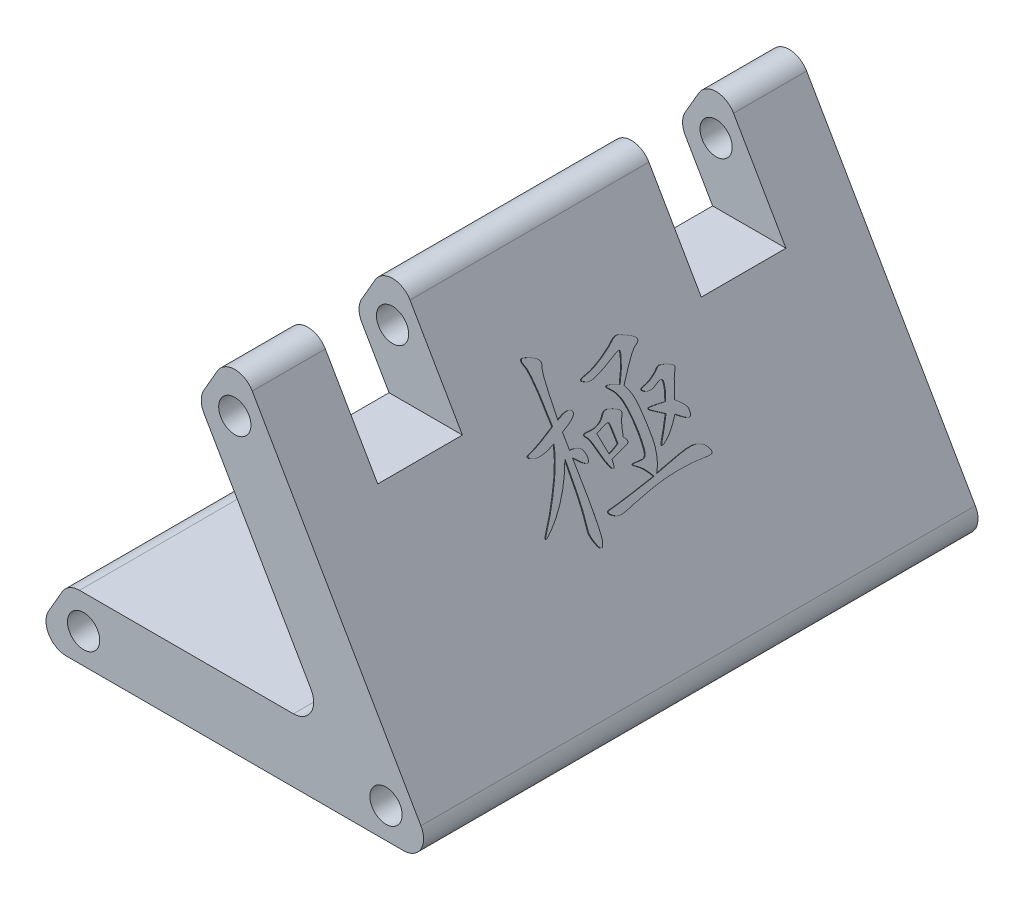
SolidWorks part; units mm, degrees
material "ABS"
ref_plane "前视基准面" through (0, 0, 0) normal (0, 0, 1) x (1, 0, 0)
ref_plane "上视基准面" through (0, 0, 0) normal (0, 1, 0) x (1, 0, 0)
ref_plane "右视基准面" through (0, 0, 0) normal (1, 0, 0) x (0, 0, -1)
sketch "草图1" plane through (0, 0, 0) normal (0, 0, 1) x (1, 0, 0)
  line L0 (0, 0) -> (-15, -25.9808) construction
  line L1 (-15, -25.9808) -> (15, -25.9808) construction
  line L2 (15, -25.9808) -> (0, 0) construction
  line L3 (20.1962, -28.9808) -> (0, 6)
  line L4 (0, 6) -> (-20.1962, -28.9808)
  line L5 (-20.1962, -28.9808) -> (20.1962, -28.9808)
  circle A0 centre (0, 0) radius 1.6
  circle A1 centre (-15, -25.9808) radius 1.6
  circle A2 centre (15, -25.9808) radius 1.6
  dimension "D3" = 3.2
  dimension "D1" = 30
  dimension "D2" = 3
extrude "凸台-拉伸1" add sketch "草图1" along normal mid plane 55
fillet "圆角1" radius 2 3 edges at (20.1962, -28.9808, 0) (-20.1962, -28.9808, 0) (0, 6, 0)
sketch "草图2" plane through (0, 0, -27.5) normal (0, 0, -1) x (-1, 0, 0)
  line L0 (3.6373, -0.3) -> (-9.2842, -22.6808)
  line L1 (1.7321, 3) -> (18.4641, -25.9808) construction
  line L2 (-9.2842, -22.6808) -> (16.5588, -22.6808)
  line L3 (16.5588, -22.6808) -> (3.6373, -0.3)
  line L4 (0, 0) -> (-15, -25.9808) construction
  circle A0 centre (15, -25.9808) radius 1.6 construction
  dimension "D1" = 3.3
  dimension "D2" = 3.3
extrude "切除-拉伸1" cut sketch "草图2" against normal mid plane 133
fillet "圆角2" radius 2 3 edges at (-16.5588, -22.6808, 0) (9.2842, -22.6808, 0) (-3.6373, -0.3, 0)
sketch "草图3" plane through (2.5981, 1.5, 0) normal (0.866, 0.5, 0) x (0, 0, -1)
  line L0 (-27.5, -19.7321) -> (27.5, -19.7321) construction
  line L1 (-27.5, -31.7321) -> (-27.5, 1.7321) construction
  line L2 (27.5, -31.7321) -> (27.5, 1.7321) construction
  line L3 (-27.5, -31.7321) -> (27.5, -31.7321) construction
  text T0 "極" font "楷体" height 12
  dimension "D1" = 12
extrude "凸台-拉伸2" add sketch "草图3" along normal mid plane 0.2
sketch "草图4" plane through (0, 0, 0) normal (1, 0, 0) x (0, 0, -1)
  line L0 (27.5, 4) -> (-27.5, 4) construction
  line L1 (-20.25, -6) -> (-11.85, -6)
  line L2 (-20.25, -6) -> (-20.25, 14)
  line L3 (-20.25, 14) -> (-11.85, 14)
  line L4 (-11.85, -6) -> (-11.85, 14)
  line L5 (-16.05, 14) -> (-16.05, -6) construction
  line L6 (-20.25, 4) -> (-11.85, 4) construction
  line L7 (0, 0) -> (0, 9.2299) construction
  line L8 (20.25, 4) -> (11.85, 4) construction
  line L9 (16.05, 14) -> (16.05, -6) construction
  line L10 (11.85, -6) -> (11.85, 14)
  line L11 (20.25, 14) -> (11.85, 14)
  line L12 (20.25, -6) -> (20.25, 14)
  line L13 (20.25, -6) -> (11.85, -6)
  point P0 (-16.05, 4)
  point P16 (16.05, 4)
  dimension "D1" = 8.4
  dimension "D2" = 32.1
  dimension "D3" = 10
extrude "切除-拉伸2" cut sketch "草图4" against normal mid plane 50
